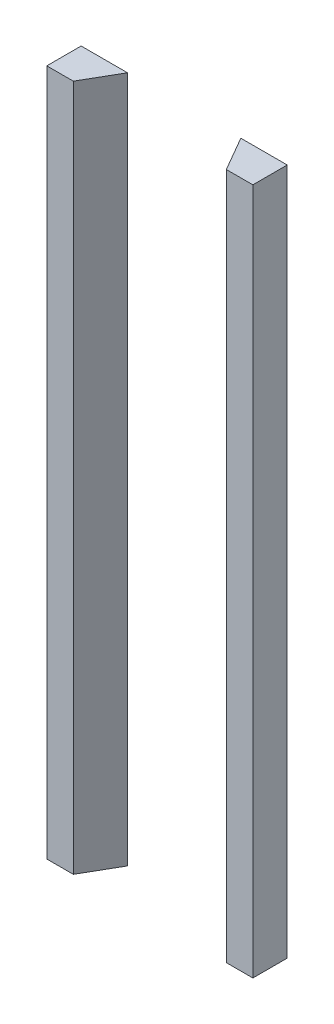
SolidWorks part; units mm, degrees
ref_plane "前视" through (0, 0, 0) normal (0, 0, 1) x (1, 0, 0)
ref_plane "上视" through (0, 0, 0) normal (0, 1, 0) x (1, 0, 0)
ref_plane "右视" through (0, 0, 0) normal (1, 0, 0) x (0, 0, -1)
sketch "草图1" plane through (0, 0, 0) normal (0, 1, 0) x (1, 0, 0)
  line L1 (-30, 5) -> (30, 5)
  line L2 (-30, 5) -> (-30, -5)
  line L3 (-30, -5) -> (30, -5)
  line L4 (30, 5) -> (30, -5)
  line L5 (-30, 5) -> (30, -5) construction
  line L6 (-30, -5) -> (30, 5) construction
  point P0 (0, 0)
  dimension "D1" = 60
  dimension "D2" = 10
extrude "凸台-拉伸1" add sketch "草图1" along normal blind 200
sketch "草图2" plane through (0, 200, 0) normal (0, 1, 0) x (1, 0, 0)
  line L0 (-22.2735, -5) -> (-16.5, 5)
  line L1 (-30, -5) -> (30, -5) construction
  line L2 (30, 5) -> (-30, 5) construction
  line L3 (-16.5, 5) -> (16.5, 5)
  line L4 (16.5, 5) -> (22.2735, -5)
  line L5 (22.2735, -5) -> (-22.2735, -5)
  line L6 (0, 5) -> (0, 0) construction
  dimension "D1" = 60
  dimension "D2" = 33
extrude "切除-拉伸1" cut sketch "草图2" against normal up to next
